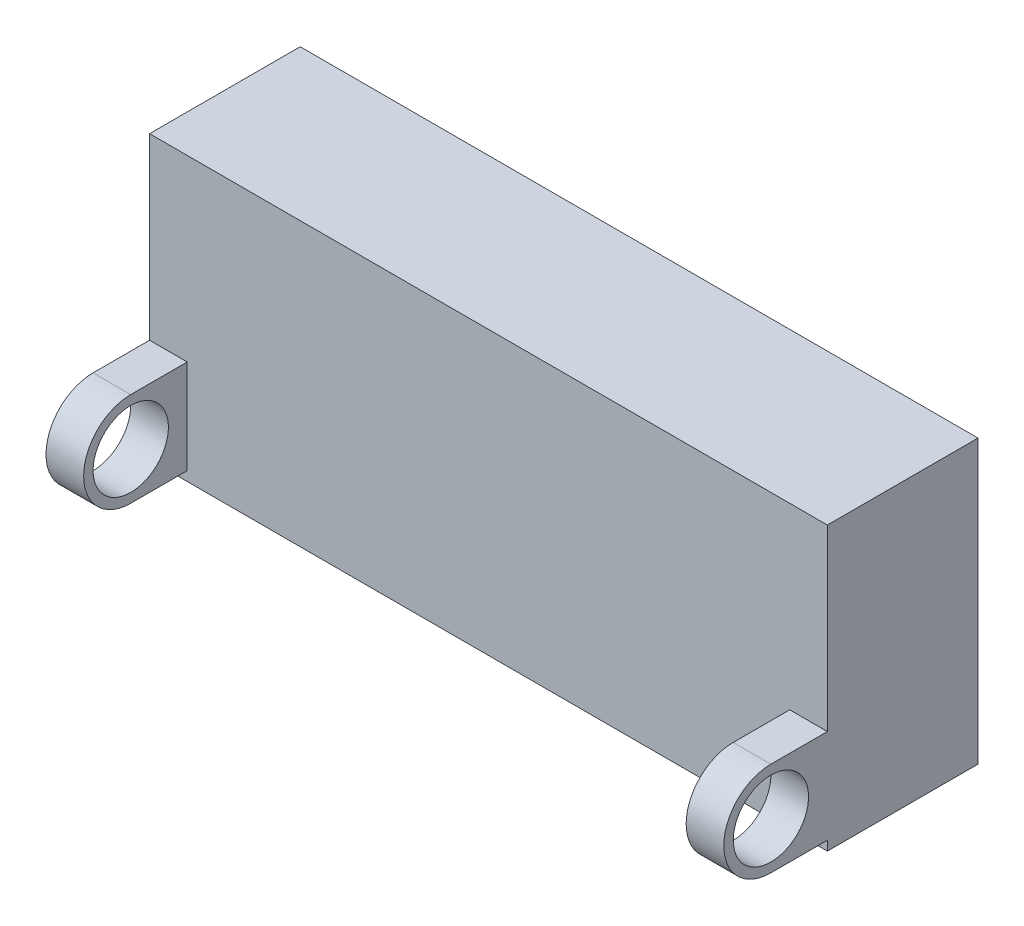
SolidWorks part; units mm, degrees
ref_plane "Plan de face" through (0, 0, 0) normal (0, 0, 1) x (1, 0, 0)
ref_plane "Plan de dessus" through (0, 0, 0) normal (0, 1, 0) x (1, 0, 0)
ref_plane "Plan de droite" through (0, 0, 0) normal (1, 0, 0) x (0, 0, -1)
sketch "Esquisse1" plane through (0, 0, 0) normal (0, 0, 1) x (1, 0, 0)
  line L1 (0, 0) -> (36, 0)
  line L2 (0, 0) -> (0, 15)
  line L3 (0, 15) -> (36, 15)
  line L4 (36, 0) -> (36, 15)
  dimension "D1" = 36
  dimension "D2" = 15
extrude "Boss.-Extru.3" add sketch "Esquisse1" along normal blind 8 contours L2 L1 L4 L3
sketch "Esquisse2" plane through (0, 0, 0) normal (-1, 0, 0) x (0, 0, 1)
  line L0 (8, 0) -> (8, 15) construction
  line L1 (8, 0) -> (0, 0) construction
  line L2 (11, 5.5) -> (8, 5.5)
  line L3 (11, 0.5) -> (8, 0.5)
  line L4 (8, 0.5) -> (8, 5.5)
  circle A0 centre (11, 3) radius 2
  arc A1 (11, 0.5) -> (11, 5.5) centre (11, 3) ccw
  dimension "D1" = 4
  dimension "D2" = 3
  dimension "D3" = 3
extrude "Boss.-Extru.4" add sketch "Esquisse2" against normal blind 2
pattern_linear "Répétition linéaire1" count 2 spacing 34 along (1, 0, 0) of "Boss.-Extru.4"
